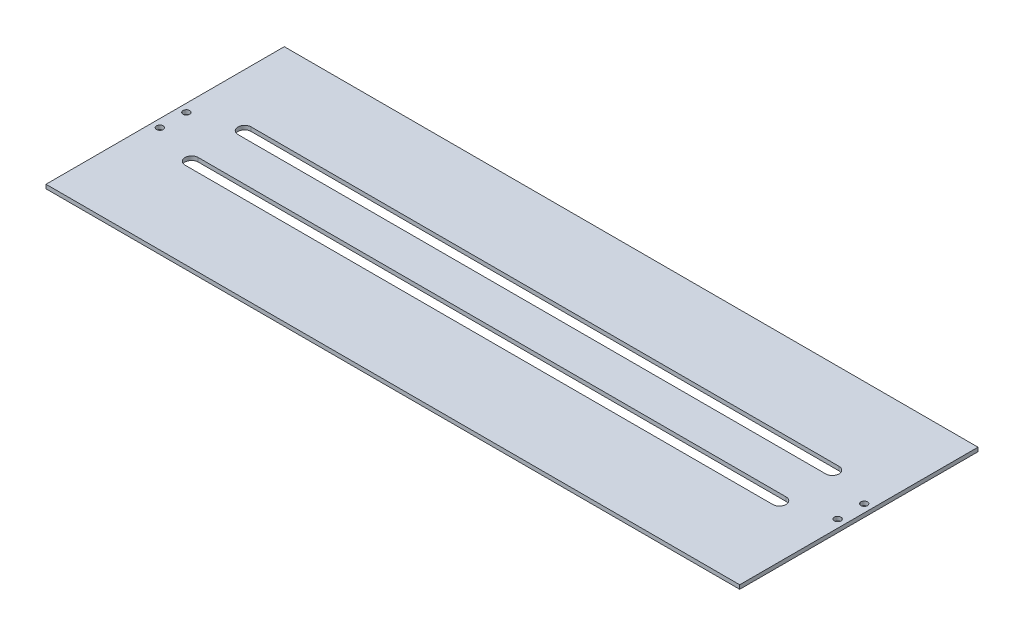
SolidWorks part; units mm, degrees
material "Acrylic (Medium-high impact)"
ref_plane "Front Plane" through (0, 0, 0) normal (0, 0, 1) x (1, 0, 0)
ref_plane "Top Plane" through (0, 0, 0) normal (0, 1, 0) x (1, 0, 0)
ref_plane "Right Plane" through (0, 0, 0) normal (1, 0, 0) x (0, 0, -1)
sketch "Sketch1" plane through (0, 0, 0) normal (0, 1, 0) x (1, 0, 0)
  line L0 (0, 90) -> (524, 90) construction
  line L1 (0, 0) -> (524, 0)
  line L2 (0, 0) -> (0, 180)
  line L3 (0, 180) -> (524, 180)
  line L4 (524, 0) -> (524, 180)
  line L5 (262, 0) -> (262, 180) construction
  dimension "D1" = 180
  dimension "D2" = 524
extrude "Boss-Extrude1" add sketch "Sketch1" along normal blind 3 contours L3 L4 L1 L2
sketch "Sketch2" plane through (0, 0, 0) normal (0, -1, 0) x (1, 0, 0)
  line L0 (0, -90) -> (524, -90) construction
  line L1 (0, 0) -> (0, -180) construction
  line L2 (524, 0) -> (524, -180) construction
  line L3 (262, -180) -> (262, 0) construction
  line L4 (0, -180) -> (524, -180) construction
  line L5 (0, 0) -> (524, 0) construction
  line L6 (484, -70) -> (40, -70) construction
  line L7 (40, -65) -> (484, -65)
  line L8 (40, -65) -> (40, -75)
  line L9 (40, -75) -> (484, -75)
  line L10 (484, -65) -> (484, -75)
  circle A0 centre (262, -70) radius 2.1 construction
  arc A1 (40, -75) -> (40, -65) centre (40, -70) cw
  arc A2 (484, -65) -> (484, -75) centre (484, -70) cw
  point P21 (0, 0)
  point P22 (262, -70)
  dimension "D1" = 4.2
  dimension "D2" = 20
  dimension "D4" = 40
  dimension "D3" = 5
extrude "Tracks" cut sketch "Sketch2" against normal through all contours A2 L10 | L10 L7 L8 L9 | A1 L8
sketch "Sketch3" plane through (0, 0, 0) normal (0, -1, 0) x (1, 0, 0)
  line L0 (0, 0) -> (0, -180) construction
  line L1 (0, -90) -> (524, -90) construction
  line L2 (262, 0) -> (262, -180) construction
  line L3 (0, 0) -> (524, 0) construction
  line L4 (0, -180) -> (524, -180) construction
  circle A0 centre (6, -80) radius 2.1 construction
  circle A1 centre (6, -80) radius 2.5
  circle A2 centre (518, -80) radius 2.1 construction
  circle A3 centre (518, -80) radius 2.5
  dimension "D1" = 4.2
  dimension "D2" = 5
  dimension "D3" = 6
  dimension "D4" = 10
extrude "screw mounting holes" cut sketch "Sketch3" against normal through all
ref_plane "Plane1" through (0, 0, -90) normal (0, 0, -1) x (-1, 0, 0)
mirror "Mirror2" about plane through (0, 0, -90) normal (0, 0, -1) of "screw mounting holes", "Tracks"
